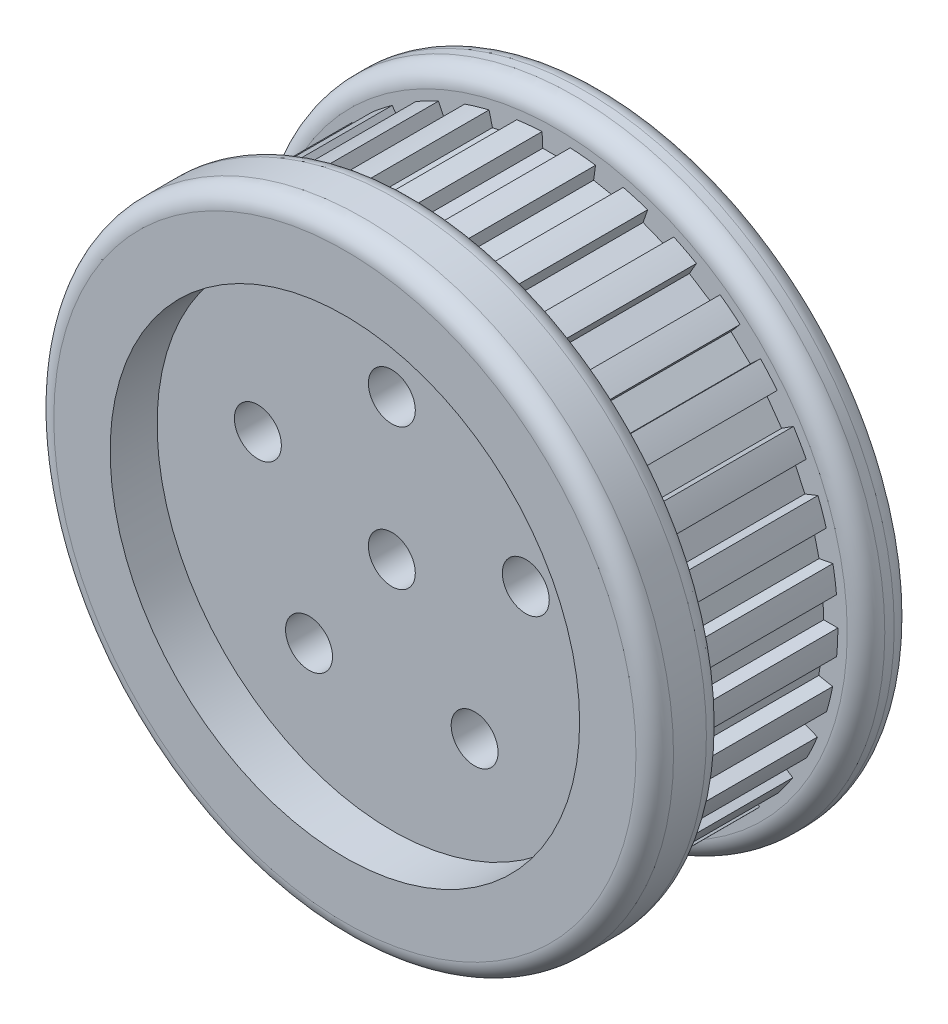
SolidWorks part; units mm, degrees
ref_plane "Front Plane" through (0, 0, 0) normal (0, 0, 1) x (1, 0, 0)
ref_plane "Top Plane" through (0, 0, 0) normal (0, 1, 0) x (1, 0, 0)
ref_plane "Right Plane" through (0, 0, 0) normal (1, 0, 0) x (0, 0, -1)
sketch "Sketch1" plane through (0, 0, 0) normal (0, 1, 0) x (1, 0, 0)
  line L0 (0, 0) -> (0, 10)
  line L1 (0, 10) -> (25, 10)
  line L2 (25, 10) -> (25, 22.5)
  line L3 (25, 22.5) -> (33, 22.5)
  line L4 (33, 22.5) -> (33, 17.5)
  line L5 (33, 17.5) -> (30, 17.5)
  line L6 (30, 17.5) -> (30, 2.5)
  line L7 (30, 2.5) -> (33, 2.5)
  line L8 (33, 2.5) -> (33, -5)
  line L9 (33, -5) -> (25, -5)
  line L10 (25, -5) -> (25, 0)
  line L11 (25, 0) -> (0, 0)
  dimension "D1" = 10
  dimension "D2" = 25
  dimension "D3" = 5
  dimension "D4" = 8
  dimension "D5" = 7.5
  dimension "D6" = 3
  dimension "D7" = 15
  dimension "D8" = 5
revolve "Revolve1" add sketch "Sketch1" angle 360 about L0
fillet "Fillet1" radius 2 4 edges at (33, 0, 5) (33, 0, -2.5) (33, 0, -17.5) (33, 0, -22.5)
sketch "Sketch2" plane through (0, 0, -10) normal (0, 0, -1) x (-1, 0, 0)
  circle A0 centre (0, 0) radius 2.5
  circle A1 centre (0, 0) radius 15 construction
  circle A2 centre (0, 15) radius 2.5
  circle A3 centre (0, 0) radius 15 construction
  circle A4 centre (14.2658, 4.6353) radius 2.5
  circle A5 centre (0, 0) radius 15 construction
  circle A6 centre (8.8168, -12.1353) radius 2.5
  circle A7 centre (0, 0) radius 15 construction
  circle A8 centre (-8.8168, -12.1353) radius 2.5
  circle A9 centre (0, 0) radius 15 construction
  circle A10 centre (-14.2658, 4.6353) radius 2.5
  point P21 (0, 0)
  dimension "D1" = 5
  dimension "D2" = 30
  dimension "D3" = 5
  dimension "D4" = 5
extrude "Cut-Extrude1" cut sketch "Sketch2" against normal through all
sketch "Sketch3" plane through (0, 0, -2.5) normal (0, 0, -1) x (-1, 0, 0)
  line L0 (-1.4249, 28.4625) -> (1.4249, 28.4625)
  line L1 (-1.4249, 28.4625) -> (-1.5, 29.9625)
  line L2 (1.4249, 28.4625) -> (1.5, 29.9625)
  circle A0 centre (0, 0) radius 30 construction
  arc A1 (1.5, 29.9625) -> (-1.5, 29.9625) centre (0, 0) ccw
  point P3 (0, 28.4625)
  dimension "D1" = 3
  dimension "D2" = 1.5
extrude "Cut-Extrude2" cut sketch "Sketch3" along normal up to surface (15 mm away) up to face at (31, 0, -17.5)
pattern_circular "CirPattern1" count 33 over 360 about axis through (0, 0, 0) along (0, 0, 1) of "Cut-Extrude2"
